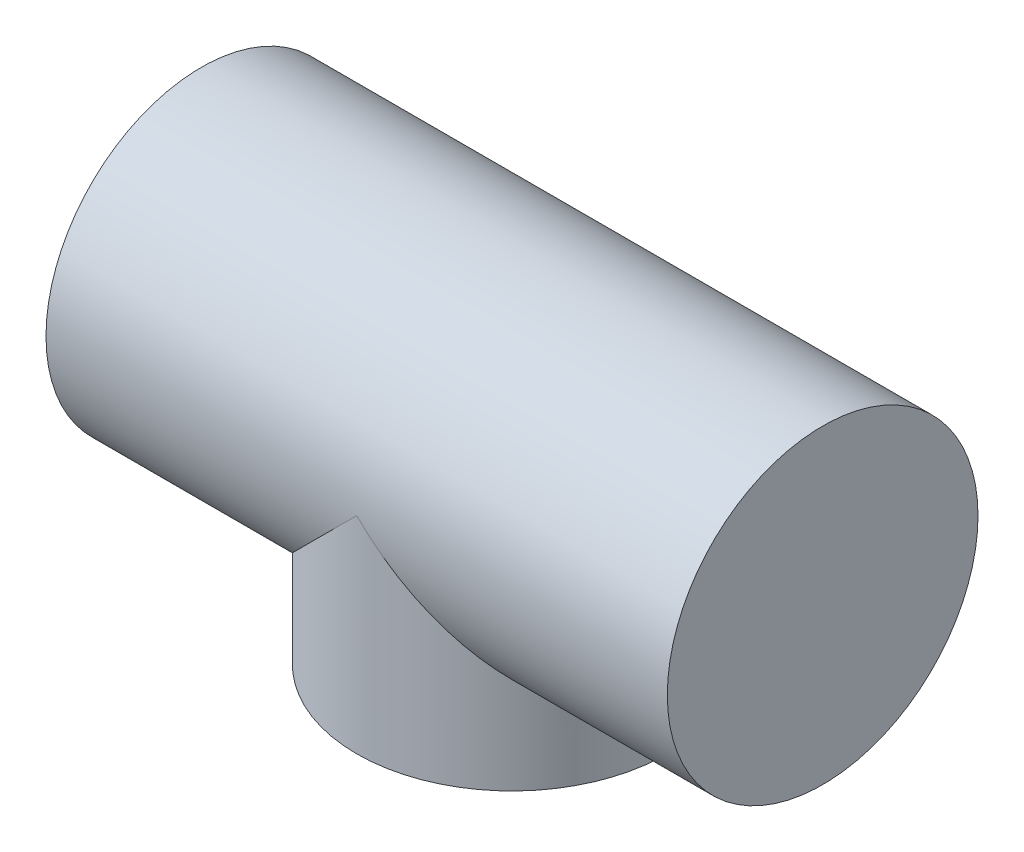
SolidWorks part; units mm, degrees
ref_plane "Front Plane" through (0, 0, 0) normal (0, 0, 1) x (1, 0, 0)
ref_plane "Top Plane" through (0, 0, 0) normal (0, 1, 0) x (1, 0, 0)
ref_plane "Right Plane" through (0, 0, 0) normal (1, 0, 0) x (0, 0, -1)
sketch "Sketch1" plane through (0, 0, 0) normal (0, 0, 1) x (1, 0, 0)
  line L0 (0, 0) -> (100, 0)
  dimension "D1" = 100
sketch "Sketch2" plane through (0, 0, 0) normal (1, 0, 0) x (0, 0, -1)
  circle A0 centre (0, 0) radius 25
  dimension "D1" = 50
sweep "Sweep1" add profiles "Sketch2" path "Sketch1"
sketch "Sketch4" plane through (0, 0, 0) normal (0, 1, 0) x (1, 0, 0)
  line L0 (0, 0) -> (100, 0) construction
  line L1 (100, -25) -> (100, 25) construction
  circle A0 centre (50, 0) radius 25
extrude "Boss-Extrude1" add sketch "Sketch4" against normal blind 33.2
